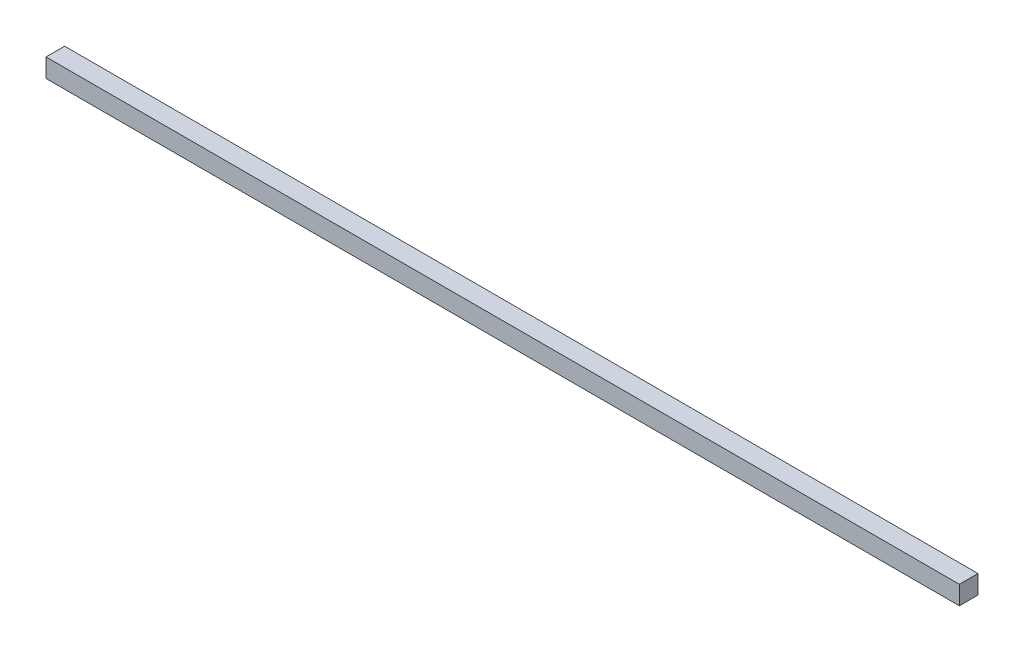
SolidWorks part; units mm, degrees
ref_plane "Front" through (0, 0, 0) normal (0, 0, 1) x (1, 0, 0)
ref_plane "Top" through (0, 0, 0) normal (0, 1, 0) x (1, 0, 0)
ref_plane "Right" through (0, 0, 0) normal (1, 0, 0) x (0, 0, -1)
sketch "草图1" plane through (0, 0, 0) normal (0, 1, 0) x (1, 0, 0)
  line L1 (-600, 12.25) -> (600, 12.25)
  line L2 (-600, 12.25) -> (-600, -12.25)
  line L3 (-600, -12.25) -> (600, -12.25)
  line L4 (600, 12.25) -> (600, -12.25)
  line L5 (-600, 12.25) -> (600, -12.25) construction
  line L6 (-600, -12.25) -> (600, 12.25) construction
  point P0 (0, 0)
  dimension "D1" = 1200
  dimension "D2" = 24.5
extrude "凸台-拉伸1" add sketch "草图1" along normal blind 24.5
